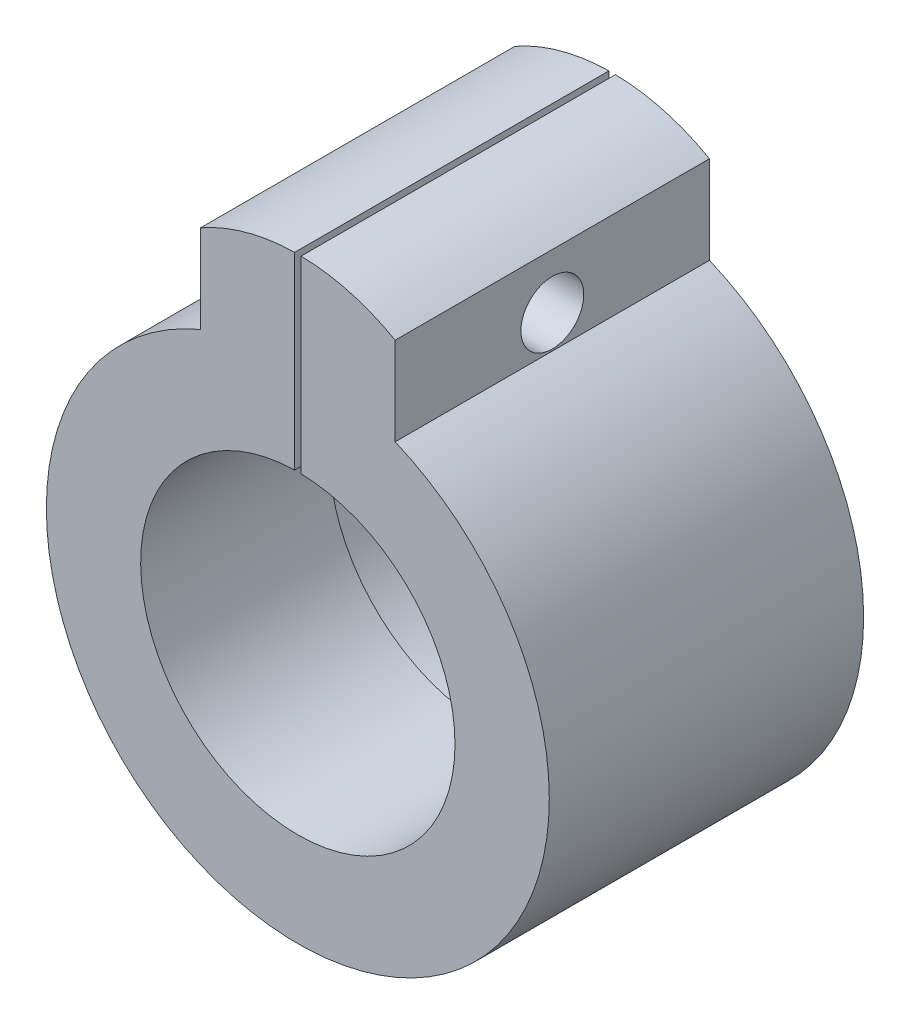
SolidWorks part; units mm, degrees
material "6061 合金"
ref_plane "前视基准面" through (0, 0, 0) normal (0, 0, 1) x (1, 0, 0)
ref_plane "上视基准面" through (0, 0, 0) normal (0, 1, 0) x (1, 0, 0)
ref_plane "右视基准面" through (0, 0, 0) normal (1, 0, 0) x (0, 0, -1)
sketch "草图1" plane through (0, 0, 0) normal (0, 0, 1) x (1, 0, 0)
  line L0 (-7.7403, 18.4415) -> (-7.7403, 25.4415)
  line L1 (-35, -7) -> (-35, 7)
  line L2 (-35, 7) -> (-7.7403, 18.4415)
  line L3 (-35, -7) -> (-7.7403, -18.4415)
  line L4 (7.7403, 18.4415) -> (7.7403, 25.4415)
  line L5 (35, -7) -> (7.7403, -18.4415)
  line L6 (35, -7) -> (35, 7)
  line L7 (35, 7) -> (7.7403, 18.4415)
  line L8 (0, 0) -> (-28, 0) construction
  circle A0 centre (0, 0) radius 13
  arc A1 (-7.7403, 18.4415) -> (7.7403, 18.4415) centre (0, 0) ccw
  arc A2 (-7.7403, 25.4415) -> (7.7403, 25.4415) centre (0, 11.8749) cw
  circle A3 centre (-28, 0) radius 3.5
  circle A4 centre (28, 0) radius 3.5
  dimension "D1" = 28
  dimension "D3" = 26
  dimension "D4" = 20
  dimension "D5" = 7
  dimension "D6" = 7
  dimension "D2" = 28
  dimension "D7" = 70
extrude "凸台-拉伸2" add sketch "草图1" along normal blind 10 contours A1 L5 L6 L7 | A2 L0 A1 L4 A0 | A1 L2 L1 L3
sketch "草图2" plane through (0, 0, 10) normal (0, 0, 1) x (1, 0, 0)
  line L0 (-7.7403, 18.4415) -> (-7.7403, 25.4415)
  line L1 (7.7403, 18.4415) -> (7.7403, 25.4415)
  circle A0 centre (0, 0) radius 12.5
  arc A1 (-7.7403, 18.4415) -> (7.7403, 18.4415) centre (0, 0) ccw
  arc A2 (-7.7403, 25.4415) -> (7.7403, 25.4415) centre (0, 11.8749) cw
extrude "凸台-拉伸3" add sketch "草图2" along normal blind 15
sketch "草图3" plane through (0, 0, 25) normal (0, 0, 1) x (1, 0, 0)
  line L1 (-0.2586, 12.3781) -> (-0.2586, 31.1043)
  line L2 (0.2586, 12.3781) -> (0.2586, 31.1043)
  line L3 (-0.2586, 12.3781) -> (0.2586, 12.3781)
  line L4 (-0.2586, 31.1043) -> (0.2586, 31.1043)
extrude "切除-拉伸1" cut sketch "草图3" against normal through all
sketch "草图4" plane through (7.7403, 0, 0) normal (1, 0, 0) x (0, 0, -1)
  circle A0 centre (-12.5, 21.0864) radius 2.5
extrude "切除-拉伸2" cut sketch "草图4" against normal through all
sketch "草图6" plane through (0, 0, 10) normal (0, 0, 1) x (1, 0, 0)
  line L3 (-7.7403, 18.4415) -> (-35, 7)
  line L4 (-35, 7) -> (-35, -7)
  line L5 (-35, -7) -> (-7.7403, -18.4415)
  line L6 (-7.7403, 18.4415) -> (-35, 7)
  line L7 (-35, 7) -> (-35, -7)
  line L8 (-35, -7) -> (-7.7403, -18.4415)
  line L9 (7.7403, -18.4415) -> (35, -7)
  line L10 (35, -7) -> (35, 7)
  line L11 (35, 7) -> (7.7403, 18.4415)
  line L12 (7.7403, -18.4415) -> (35, -7)
  line L13 (35, -7) -> (35, 7)
  line L14 (35, 7) -> (7.7403, 18.4415)
  arc A1 (-7.7403, 18.4415) -> (-7.7403, -18.4415) centre (0, 0) ccw
  arc A2 (-7.7403, 18.4415) -> (-7.7403, -18.4415) centre (0, 0) ccw
  arc A3 (7.7403, -18.4415) -> (7.7403, 18.4415) centre (0, 0) ccw
  arc A4 (7.7403, -18.4415) -> (7.7403, 18.4415) centre (0, 0) ccw
  dimension "D1" = 0
  dimension "D2" = 0
extrude "切除-拉伸3" cut sketch "草图6" against normal blind 10
